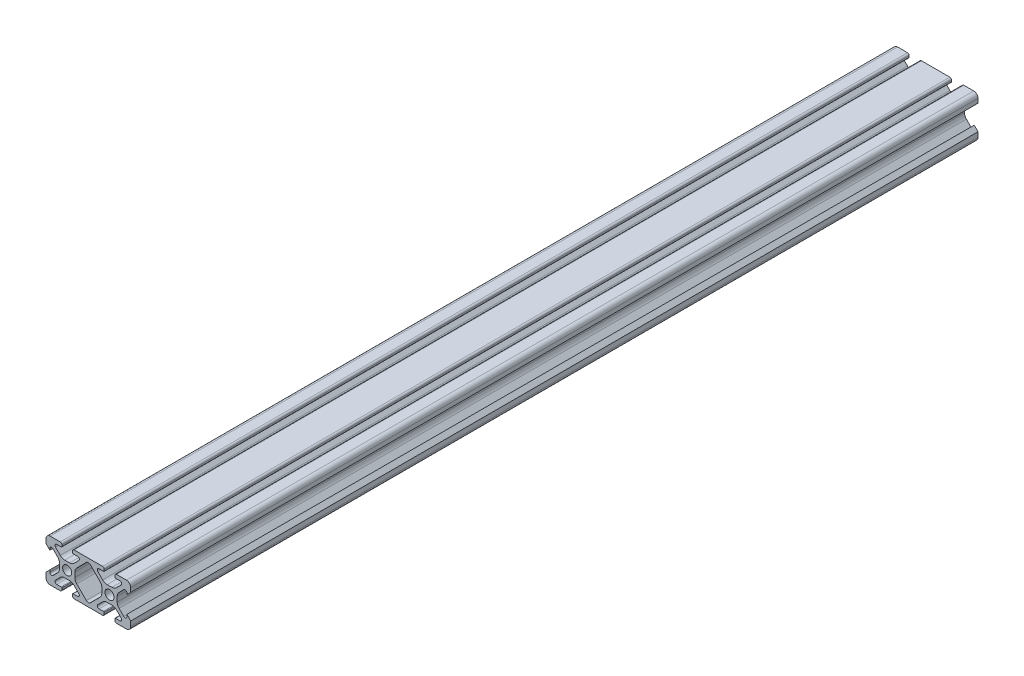
SolidWorks part; units mm, degrees
ref_plane "Front Plane" through (0, 0, 0) normal (0, 0, 1) x (1, 0, 0)
ref_plane "Top Plane" through (0, 0, 0) normal (0, 1, 0) x (1, 0, 0)
ref_plane "Right Plane" through (0, 0, 0) normal (1, 0, 0) x (0, 0, -1)
sketch "Sketch1" plane through (0, 0, 0) normal (0, 0, 1) x (1, 0, 0)
  line L2 (-19.9898, 7.9883) -> (-19.9898, 3.2893)
  line L3 (-17.9832, 9.9949) -> (-13.2842, 9.9949)
  line L4 (-12.4968, 9.2075) -> (-12.4968, 8.4963)
  line L5 (-12.8016, 8.1915) -> (-14.9098, 8.1915)
  line L6 (-15.5025, 6.7606) -> (-13.2477, 4.5058)
  line L7 (-16.7555, 5.5076) -> (-14.5007, 3.2528)
  line L8 (-18.1864, 4.9149) -> (-18.1864, 2.8067)
  line L9 (-18.4912, 2.5019) -> (-19.2024, 2.5019)
  line L11 (-11.1283, 3.6279) -> (-8.8615, 3.6279)
  line L12 (-13.6228, 1.1334) -> (-13.6228, -1.1334)
  line L13 (0, 9.9949) -> (-6.7056, 9.9949)
  line L14 (-7.493, 9.2075) -> (-7.493, 8.4963)
  line L15 (-7.1882, 8.1915) -> (-5.08, 8.1915)
  line L16 (-6.367, 1.1334) -> (-6.367, -1.1334)
  line L17 (-4.4873, 6.7606) -> (-6.7421, 4.5058)
  line L18 (-0.9396, 7.8023) -> (-5.4891, 3.2528)
  line L19 (-18.4912, -2.5019) -> (-19.2024, -2.5019)
  line L20 (-18.1864, -4.9149) -> (-18.1864, -2.8067)
  line L21 (-16.7555, -5.5076) -> (-14.5007, -3.2528)
  line L22 (-15.5025, -6.7606) -> (-13.2477, -4.5058)
  line L23 (-12.8016, -8.1915) -> (-14.9098, -8.1915)
  line L24 (-12.4968, -9.2075) -> (-12.4968, -8.4963)
  line L25 (-17.9832, -9.9949) -> (-13.2842, -9.9949)
  line L26 (-19.9898, -7.9883) -> (-19.9898, -3.2893)
  line L27 (0, -9.9949) -> (-6.7056, -9.9949)
  line L28 (-7.493, -9.2075) -> (-7.493, -8.4963)
  line L29 (-7.1882, -8.1915) -> (-5.08, -8.1915)
  line L30 (-4.4873, -6.7606) -> (-6.7421, -4.5058)
  line L31 (-0.9396, -7.8023) -> (-5.4891, -3.2528)
  line L32 (-11.1283, -3.6279) -> (-8.8615, -3.6279)
  line L34 (11.1283, -3.6279) -> (8.8615, -3.6279)
  line L35 (0.9396, -7.8023) -> (5.4891, -3.2528)
  line L36 (4.4873, -6.7606) -> (6.7421, -4.5058)
  line L37 (7.1882, -8.1915) -> (5.08, -8.1915)
  line L38 (7.493, -9.2075) -> (7.493, -8.4963)
  line L39 (0, -9.9949) -> (6.7056, -9.9949)
  line L40 (19.9898, -7.9883) -> (19.9898, -3.2893)
  line L41 (17.9832, -9.9949) -> (13.2842, -9.9949)
  line L42 (12.4968, -9.2075) -> (12.4968, -8.4963)
  line L43 (12.8016, -8.1915) -> (14.9098, -8.1915)
  line L44 (15.5025, -6.7606) -> (13.2477, -4.5058)
  line L45 (16.7555, -5.5076) -> (14.5007, -3.2528)
  line L46 (18.1864, -4.9149) -> (18.1864, -2.8067)
  line L47 (18.4912, -2.5019) -> (19.2024, -2.5019)
  line L48 (0.9396, 7.8023) -> (5.4891, 3.2528)
  line L49 (4.4873, 6.7606) -> (6.7421, 4.5058)
  line L50 (6.367, 1.1334) -> (6.367, -1.1334)
  line L51 (7.1882, 8.1915) -> (5.08, 8.1915)
  line L52 (7.493, 9.2075) -> (7.493, 8.4963)
  line L53 (0, 9.9949) -> (6.7056, 9.9949)
  line L54 (13.6228, 1.1334) -> (13.6228, -1.1334)
  line L55 (11.1283, 3.6279) -> (8.8615, 3.6279)
  line L56 (18.4912, 2.5019) -> (19.2024, 2.5019)
  line L57 (18.1864, 4.9149) -> (18.1864, 2.8067)
  line L58 (16.7555, 5.5076) -> (14.5007, 3.2528)
  line L59 (15.5025, 6.7606) -> (13.2477, 4.5058)
  line L60 (12.8016, 8.1915) -> (14.9098, 8.1915)
  line L61 (12.4968, 9.2075) -> (12.4968, 8.4963)
  line L62 (17.9832, 9.9949) -> (13.2842, 9.9949)
  line L63 (19.9898, 7.9883) -> (19.9898, 3.2893)
  circle A0 centre (-9.9949, 0) radius 2.1463
  arc A1 (-19.9898, 7.9883) -> (-17.9832, 9.9949) centre (-17.9832, 7.9883) cw
  arc A2 (-16.7555, 5.5076) -> (-18.1864, 4.9149) centre (-17.3482, 4.9149) ccw
  arc A3 (-14.9098, 8.1915) -> (-15.5025, 6.7606) centre (-14.9098, 7.3533) ccw
  arc A4 (-13.2842, 9.9949) -> (-12.4968, 9.2075) centre (-13.2842, 9.2075) cw
  arc A5 (-19.9898, 3.2893) -> (-19.2024, 2.5019) centre (-19.2024, 3.2893) ccw
  arc A6 (-18.1864, 2.8067) -> (-18.4912, 2.5019) centre (-18.4912, 2.8067) cw
  arc A7 (-12.4968, 8.4963) -> (-12.8016, 8.1915) centre (-12.8016, 8.4963) cw
  arc A8 (-11.1283, 3.6279) -> (-13.2477, 4.5058) centre (-11.1283, 6.6251) cw
  arc A9 (-13.6228, 1.1334) -> (-14.5007, 3.2528) centre (-16.62, 1.1334) ccw
  arc A10 (0.9396, 7.8023) -> (-0.9396, 7.8023) centre (0, 6.8627) ccw
  arc A11 (-0.9396, -7.8023) -> (0.9396, -7.8023) centre (0, -6.8627) ccw
  arc A12 (-6.7056, 9.9949) -> (-7.493, 9.2075) centre (-6.7056, 9.2075) ccw
  arc A13 (-7.493, 8.4963) -> (-7.1882, 8.1915) centre (-7.1882, 8.4963) ccw
  arc A14 (-8.8615, 3.6279) -> (-6.7421, 4.5058) centre (-8.8615, 6.6251) ccw
  arc A15 (-6.367, 1.1334) -> (-5.4891, 3.2528) centre (-3.3698, 1.1334) cw
  arc A16 (-5.08, 8.1915) -> (-4.4873, 6.7606) centre (-5.08, 7.3533) cw
  arc A17 (-13.6228, -1.1334) -> (-14.5007, -3.2528) centre (-16.62, -1.1334) cw
  arc A18 (-11.1283, -3.6279) -> (-13.2477, -4.5058) centre (-11.1283, -6.6251) ccw
  arc A19 (-12.4968, -8.4963) -> (-12.8016, -8.1915) centre (-12.8016, -8.4963) ccw
  arc A20 (-18.1864, -2.8067) -> (-18.4912, -2.5019) centre (-18.4912, -2.8067) ccw
  arc A21 (-19.9898, -3.2893) -> (-19.2024, -2.5019) centre (-19.2024, -3.2893) cw
  arc A22 (-13.2842, -9.9949) -> (-12.4968, -9.2075) centre (-13.2842, -9.2075) ccw
  arc A23 (-14.9098, -8.1915) -> (-15.5025, -6.7606) centre (-14.9098, -7.3533) cw
  arc A24 (-16.7555, -5.5076) -> (-18.1864, -4.9149) centre (-17.3482, -4.9149) cw
  arc A25 (-19.9898, -7.9883) -> (-17.9832, -9.9949) centre (-17.9832, -7.9883) ccw
  arc A26 (-5.08, -8.1915) -> (-4.4873, -6.7606) centre (-5.08, -7.3533) ccw
  arc A27 (-6.7056, -9.9949) -> (-7.493, -9.2075) centre (-6.7056, -9.2075) cw
  arc A28 (-7.493, -8.4963) -> (-7.1882, -8.1915) centre (-7.1882, -8.4963) cw
  arc A29 (-8.8615, -3.6279) -> (-6.7421, -4.5058) centre (-8.8615, -6.6251) cw
  arc A30 (-6.367, -1.1334) -> (-5.4891, -3.2528) centre (-3.3698, -1.1334) ccw
  arc A31 (6.367, -1.1334) -> (5.4891, -3.2528) centre (3.3698, -1.1334) cw
  arc A32 (8.8615, -3.6279) -> (6.7421, -4.5058) centre (8.8615, -6.6251) ccw
  arc A33 (7.493, -8.4963) -> (7.1882, -8.1915) centre (7.1882, -8.4963) ccw
  arc A34 (6.7056, -9.9949) -> (7.493, -9.2075) centre (6.7056, -9.2075) ccw
  arc A35 (5.08, -8.1915) -> (4.4873, -6.7606) centre (5.08, -7.3533) cw
  arc A36 (19.9898, -7.9883) -> (17.9832, -9.9949) centre (17.9832, -7.9883) cw
  arc A37 (16.7555, -5.5076) -> (18.1864, -4.9149) centre (17.3482, -4.9149) ccw
  arc A38 (14.9098, -8.1915) -> (15.5025, -6.7606) centre (14.9098, -7.3533) ccw
  arc A39 (13.2842, -9.9949) -> (12.4968, -9.2075) centre (13.2842, -9.2075) cw
  arc A40 (19.9898, -3.2893) -> (19.2024, -2.5019) centre (19.2024, -3.2893) ccw
  arc A41 (18.1864, -2.8067) -> (18.4912, -2.5019) centre (18.4912, -2.8067) cw
  arc A42 (12.4968, -8.4963) -> (12.8016, -8.1915) centre (12.8016, -8.4963) cw
  arc A43 (11.1283, -3.6279) -> (13.2477, -4.5058) centre (11.1283, -6.6251) cw
  arc A44 (13.6228, -1.1334) -> (14.5007, -3.2528) centre (16.62, -1.1334) ccw
  arc A45 (5.08, 8.1915) -> (4.4873, 6.7606) centre (5.08, 7.3533) ccw
  arc A46 (6.367, 1.1334) -> (5.4891, 3.2528) centre (3.3698, 1.1334) ccw
  arc A47 (8.8615, 3.6279) -> (6.7421, 4.5058) centre (8.8615, 6.6251) cw
  arc A48 (7.493, 8.4963) -> (7.1882, 8.1915) centre (7.1882, 8.4963) cw
  arc A49 (6.7056, 9.9949) -> (7.493, 9.2075) centre (6.7056, 9.2075) cw
  arc A50 (13.6228, 1.1334) -> (14.5007, 3.2528) centre (16.62, 1.1334) cw
  arc A51 (11.1283, 3.6279) -> (13.2477, 4.5058) centre (11.1283, 6.6251) ccw
  arc A52 (12.4968, 8.4963) -> (12.8016, 8.1915) centre (12.8016, 8.4963) ccw
  arc A53 (18.1864, 2.8067) -> (18.4912, 2.5019) centre (18.4912, 2.8067) ccw
  arc A54 (19.9898, 3.2893) -> (19.2024, 2.5019) centre (19.2024, 3.2893) cw
  arc A55 (13.2842, 9.9949) -> (12.4968, 9.2075) centre (13.2842, 9.2075) ccw
  arc A56 (14.9098, 8.1915) -> (15.5025, 6.7606) centre (14.9098, 7.3533) cw
  arc A57 (16.7555, 5.5076) -> (18.1864, 4.9149) centre (17.3482, 4.9149) cw
  arc A58 (19.9898, 7.9883) -> (17.9832, 9.9949) centre (17.9832, 7.9883) ccw
  circle A59 centre (9.9949, 0) radius 2.1463
  point P186 (9.9949, 3.6279)
extrude "Boss-Extrude1" add sketch "Sketch1" along normal blind 400
sketch "Sketch2" plane through (0, 0, 400) normal (0, 0, 1) x (1, 0, 0)
  line L0 (-20.3609, 6.3448) -> (-17.1578, 3.1417)
  line L1 (-17.1578, -2.8583) -> (-17.1578, 3.1417)
  line L2 (-17.1578, -2.8583) -> (-20.3609, -6.0614)
  line L3 (-20.3609, -6.0614) -> (-20.3609, 6.3448)
  line L4 (-1023.8938, 3.1417) -> (-19.9898, 3.1417) construction
  line L5 (983.9142, -2.8583) -> (-19.9898, -2.8583) construction
  line L9 (0, 0) -> (-17.1578, 0) construction
  line L10 (0, 0) -> (0, -12.8324) construction
  line L11 (17.1578, -2.8583) -> (20.3609, -6.0614)
  line L12 (17.1578, -2.8583) -> (17.1578, 3.1417)
  line L13 (20.3609, 6.3448) -> (17.1578, 3.1417)
  line L14 (20.3609, -6.0614) -> (20.3609, 6.3448)
  line L16 (-17.1578, 3.1417) -> (25.527, 3.1417) construction
  line L17 (-19.9898, 0) -> (-33.0483, 0) construction
  line L18 (-20.3609, -2.8583) -> (-31.5313, -2.8583) construction
  dimension "D1" = 45
  dimension "D2" = 45
  dimension "D4" = 6
extrude "Cut-Extrude1" cut sketch "Sketch2" against normal through all
